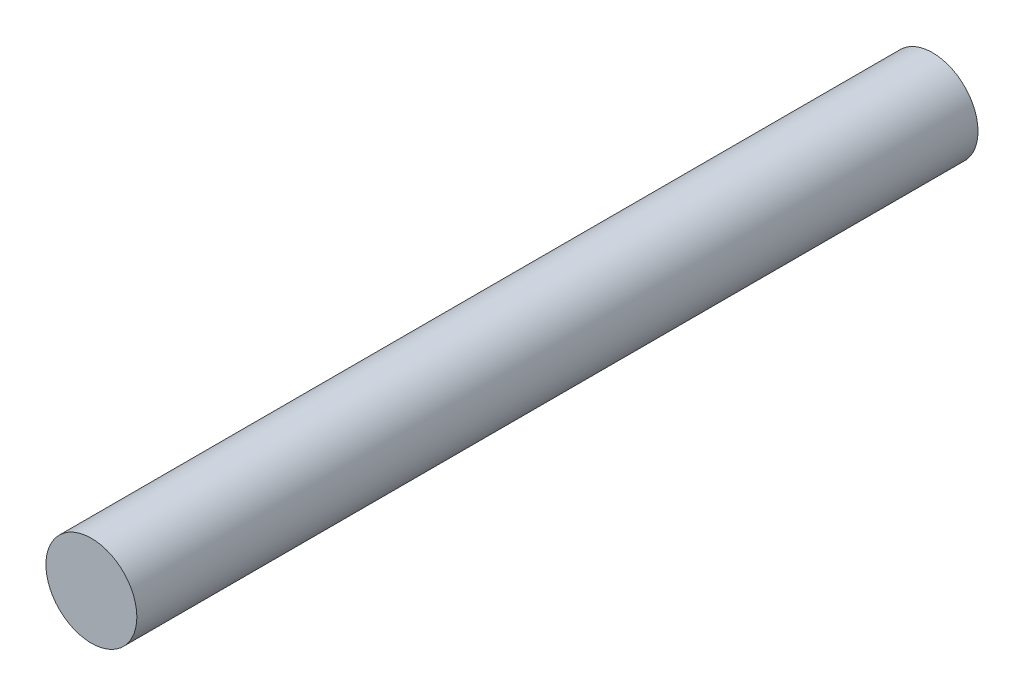
SolidWorks part; units mm, degrees
ref_plane "Front Plane" through (0, 0, 0) normal (0, 0, 1) x (1, 0, 0)
ref_plane "Top Plane" through (0, 0, 0) normal (0, 1, 0) x (1, 0, 0)
ref_plane "Right Plane" through (0, 0, 0) normal (1, 0, 0) x (0, 0, -1)
sketch "Sketch1" plane through (0, 0, 0) normal (0, 0, 1) x (1, 0, 0)
  circle A0 centre (0, 0) radius 25.4
  dimension "D1" = 50.8
extrude "Boss-Extrude1" add sketch "Sketch1" along normal mid plane 469.9
